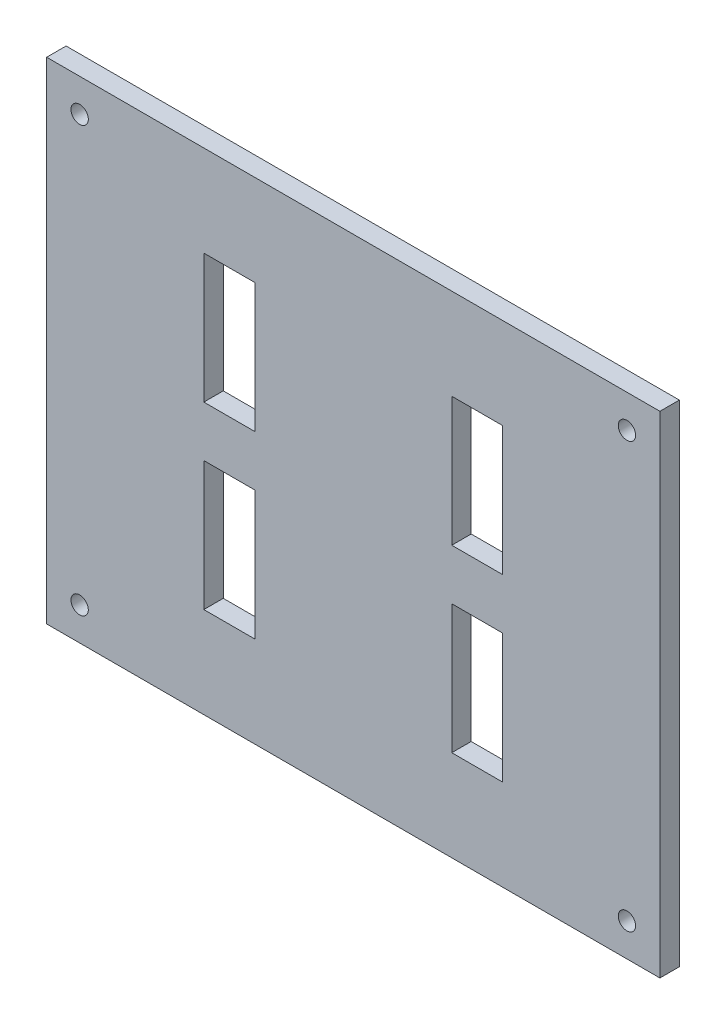
SolidWorks part; units mm, degrees
material "Maple"
ref_plane "Front Plane" through (0, 0, 0) normal (0, 0, 1) x (1, 0, 0)
ref_plane "Top Plane" through (0, 0, 0) normal (0, 1, 0) x (1, 0, 0)
ref_plane "Right Plane" through (0, 0, 0) normal (1, 0, 0) x (0, 0, -1)
sketch "Sketch1" plane through (0, 0, 0) normal (0, 0, 1) x (1, 0, 0)
  line L1 (-50.085, 40.085) -> (50.085, 40.085)
  line L2 (-50.085, 40.085) -> (-50.085, -40.085)
  line L3 (-50.085, -40.085) -> (50.085, -40.085)
  line L4 (50.085, 40.085) -> (50.085, -40.085)
  line L5 (-50.085, 40.085) -> (50.085, -40.085) construction
  line L6 (-50.085, -40.085) -> (50.085, 40.085) construction
  point P0 (0, 0)
  dimension "D1" = 100.17
  dimension "D2" = 80.17
extrude "Boss-Extrude1" add sketch "Sketch1" along normal blind 3.175
sketch "Sketch2" plane through (0, 0, 3.175) normal (0, 0, 1) x (1, 0, 0)
  line L0 (-35.3, 25.3) -> (-35.3, -25.3) construction
  line L1 (-37.3, 27.3) -> (37.3, 27.3) construction
  line L2 (-37.3, 27.3) -> (-37.3, -27.3) construction
  line L3 (-37.3, -27.3) -> (37.3, -27.3) construction
  line L4 (37.3, 27.3) -> (37.3, -27.3) construction
  line L5 (-37.3, 27.3) -> (37.3, -27.3) construction
  line L6 (-37.3, -27.3) -> (37.3, 27.3) construction
  line L7 (-35.3, -25.3) -> (35.3, -25.3) construction
  line L8 (35.3, 25.3) -> (35.3, -25.3) construction
  line L9 (-35.3, 25.3) -> (35.3, 25.3) construction
  line L10 (35.3, 0) -> (16, 0) construction
  line L11 (16, 0) -> (16, 25.3) construction
  line L12 (16, -4.05) -> (24.5, -4.05)
  line L13 (16, 25.3) -> (24.5, 25.3)
  line L14 (16, 25.3) -> (16, 4.05)
  line L15 (16, 4.05) -> (24.5, 4.05)
  line L16 (24.5, 25.3) -> (24.5, 4.05)
  line L17 (24.5, -25.3) -> (24.5, -4.05)
  line L18 (16, -25.3) -> (24.5, -25.3)
  line L19 (16, -25.3) -> (16, -4.05)
  line L20 (0, 0) -> (0, -8.4087) construction
  line L21 (-16, -25.3) -> (-16, -4.05)
  line L22 (-16, -25.3) -> (-24.5, -25.3)
  line L23 (-24.5, -25.3) -> (-24.5, -4.05)
  line L24 (-16, -4.05) -> (-24.5, -4.05)
  line L25 (-16, 4.05) -> (-24.5, 4.05)
  line L26 (-24.5, 25.3) -> (-24.5, 4.05)
  line L27 (-16, 25.3) -> (-24.5, 25.3)
  line L28 (-16, 25.3) -> (-16, 4.05)
  line L29 (-16.085, 25.215) -> (-24.415, 25.215)
  line L30 (-24.415, 25.215) -> (-24.415, 4.135)
  line L31 (-16.085, 4.135) -> (-24.415, 4.135)
  line L32 (-16.085, 25.215) -> (-16.085, 4.135)
  line L33 (16.085, 25.215) -> (16.085, 4.135)
  line L34 (16.085, 4.135) -> (24.415, 4.135)
  line L35 (24.415, 25.215) -> (24.415, 4.135)
  line L36 (16.085, 25.215) -> (24.415, 25.215)
  line L37 (-16.085, -25.215) -> (-16.085, -4.135)
  line L38 (-16.085, -4.135) -> (-24.415, -4.135)
  line L39 (-24.415, -25.215) -> (-24.415, -4.135)
  line L40 (-16.085, -25.215) -> (-24.415, -25.215)
  line L41 (16.085, -4.135) -> (24.415, -4.135)
  line L42 (24.415, -25.215) -> (24.415, -4.135)
  line L43 (16.085, -25.215) -> (24.415, -25.215)
  line L44 (16.085, -25.215) -> (16.085, -4.135)
  point P0 (0, 0)
  point P12 (29.05, 0)
  dimension "D1" = 74.6
  dimension "D2" = 54.6
  dimension "D4" = 19.3
  dimension "D5" = 6.25
  dimension "D6" = 8.5
  dimension "D7" = 21.25
  dimension "D3" = 2
  dimension "D8" = 0.085
  dimension "D9" = 0.085
  dimension "D10" = 0.085
  dimension "D11" = 0.085
sketch "Sketch3" plane through (0, 0, 3.175) normal (0, 0, 1) x (1, 0, 0)
  line L0 (-44.6967, 34.6967) -> (-50, 40) construction
  line L3 (0, 0) -> (0, -11.0646) construction
  line L4 (0, 0) -> (-7.9255, 0) construction
  line L9 (-50, 40) -> (-50, -40.085)
  line L10 (50.085, 40) -> (-50, 40)
  line L11 (-50, 40) -> (-50, -40.085) construction
  line L12 (50.085, 40) -> (-50, 40) construction
  circle A0 centre (-44.6967, 34.6967) radius 1.415
  circle A1 centre (44.6967, 34.6967) radius 1.415
  circle A2 centre (44.6967, -34.6967) radius 1.415
  circle A3 centre (-44.6967, -34.6967) radius 1.415
  dimension "D3" = 2.83
  dimension "D1" = 7.5
  dimension "D2" = 45
  dimension "D4" = 0.085
extrude "Cut-Extrude2" cut sketch "Sketch3" against normal through all
extrude "Cut-Extrude3" cut sketch "Sketch2" against normal blind 10 contours L29 L30 L31 L32 | L33 L34 L35 L36 | L41 L42 L43 L44 | L37 L38 L39 L40
equation "\"length\"= 100mm"
equation "\"width\"= 80mm"
equation "\"depth\"= 6.35mm"
equation "\"D1@Sketch2\"=\"length\"- 4*\"depth\""
equation "\"D2@Sketch2\"=\"width\"- 4*\"depth\""
equation "\"depth2\"= 6.35 / 2"
equation "\"D1@Boss-Extrude1\"=\"depth2\""
equation "\"kerf\"= 0.17 / 2"
